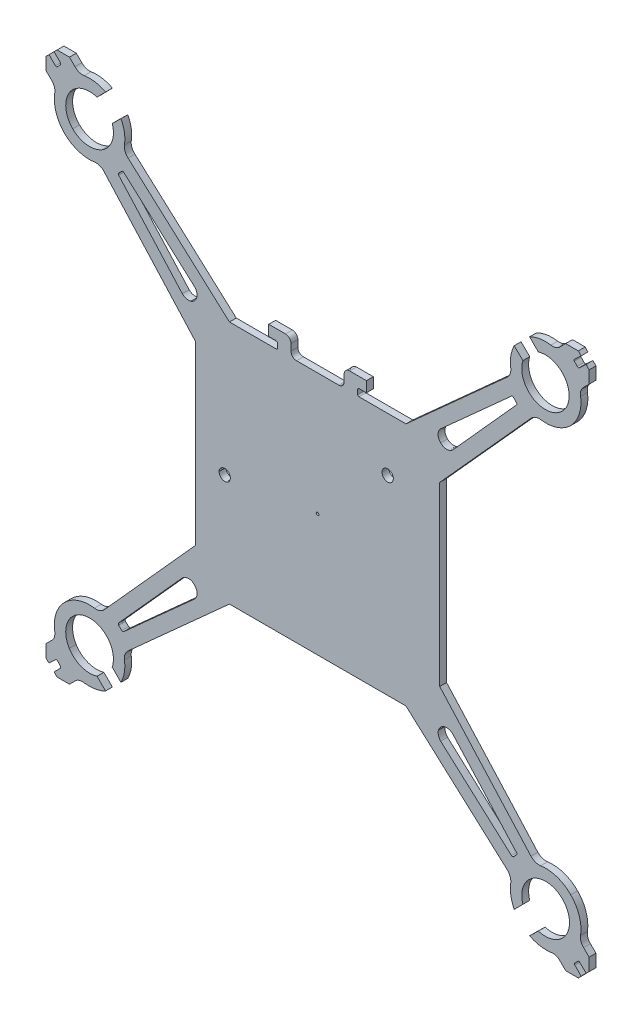
SolidWorks part; units mm, degrees
ref_plane "前视基准面" through (0, 0, 0) normal (0, 0, 1) x (1, 0, 0)
ref_plane "上视基准面" through (0, 0, 0) normal (0, 1, 0) x (1, 0, 0)
ref_plane "右视基准面" through (0, 0, 0) normal (1, 0, 0) x (0, 0, -1)
sketch "Model" plane through (0, 0, 0) normal (0, 0, 1) x (1, 0, 0)
  line L5 (274.707, 225.9985) -> (272.592, 225.9985)
  line L6 (271.5768, 227.0137) -> (271.5768, 228.2404)
  line L7 (270.5616, 229.2556) -> (267.4737, 229.2556)
  line L8 (267.4737, 229.2556) -> (267.4737, 227.3098)
  line L9 (267.4737, 227.3098) -> (268.8273, 227.3098)
  line L10 (269.0811, 227.056) -> (269.0811, 226.2523)
  line L11 (268.8273, 225.9985) -> (260.2404, 225.9985)
  line L12 (260.2404, 225.9985) -> (241.5861, 242.7916)
  line L13 (240.2748, 248.4175) -> (238.6674, 246.8524)
  line L14 (235.8756, 249.6442) -> (237.4407, 251.2516)
  line L15 (231.8148, 252.4783) -> (230.7996, 253.4935)
  line L16 (230.7996, 253.4935) -> (228.5154, 253.4935)
  line L17 (228.5154, 253.4935) -> (227.9655, 252.9436)
  line L18 (227.9655, 252.9436) -> (229.1499, 251.7592)
  line L19 (228.2193, 250.8286) -> (227.0349, 252.013)
  line L20 (227.0349, 252.013) -> (226.485, 251.4631)
  line L21 (226.485, 251.4631) -> (226.485, 249.1789)
  line L22 (226.485, 249.1789) -> (227.5002, 248.1637)
  line L23 (237.1869, 238.3924) -> (253.98, 219.7804)
  line L87 (253.98, 187.2517) -> (237.1869, 168.5974)
  line L88 (227.5002, 158.8684) -> (226.485, 157.8532)
  line L89 (226.485, 157.8532) -> (226.485, 155.5267)
  line L90 (226.485, 155.5267) -> (227.0349, 155.0191)
  line L91 (227.0349, 155.0191) -> (228.2193, 156.1612)
  line L92 (229.1499, 155.2729) -> (227.9655, 154.0885)
  line L93 (227.9655, 154.0885) -> (228.5154, 153.5386)
  line L94 (228.5154, 153.5386) -> (230.7996, 153.5386)
  line L95 (230.7996, 153.5386) -> (231.8148, 154.5538)
  line L96 (237.4407, 155.7805) -> (235.8756, 157.3456)
  line L97 (238.6674, 160.1797) -> (240.2748, 158.5723)
  line L98 (241.5861, 164.2405) -> (260.2404, 181.0336)
  line L99 (260.2404, 181.0336) -> (292.7268, 181.0336)
  line L100 (311.3811, 164.2405) -> (292.7268, 181.0336)
  line L101 (274.707, 225.9985) -> (278.2179, 225.9985)
  line L102 (253.98, 219.7804) -> (253.98, 187.2517)
  line L103 (298.9449, 219.7804) -> (298.9449, 187.2517)
  line L104 (253.98, 203.5161) -> (298.9449, 203.5161) construction
  line L105 (276.4624, 225.9985) -> (276.4836, 181.0336) construction
  line L106 (323.7307, 251.4898) -> (324.2582, 250.9184)
  line L107 (228.6, 250.8709) -> (229.1076, 251.4208)
  line L108 (239.8518, 239.5345) -> (240.444, 240.1267)
  line L109 (312.6501, 158.5723) -> (314.2575, 160.1797)
  line L110 (317.0916, 157.3456) -> (315.4842, 155.7805)
  line L111 (321.1101, 154.5538) -> (322.1253, 153.5386)
  line L112 (322.1253, 153.5386) -> (324.4518, 153.5386)
  line L113 (324.4518, 153.5386) -> (324.9594, 154.0885)
  line L114 (324.9594, 154.0885) -> (323.8173, 155.2729)
  line L115 (324.7056, 156.1612) -> (325.89, 155.0191)
  line L116 (325.89, 155.0191) -> (326.4399, 155.5267)
  line L117 (326.4399, 155.5267) -> (326.4399, 157.8532)
  line L118 (326.4399, 157.8532) -> (325.4247, 158.8684)
  line L119 (315.738, 168.5974) -> (298.9449, 187.2517)
  line L183 (298.9449, 219.7804) -> (315.738, 238.3924)
  line L184 (325.4247, 248.1637) -> (326.4399, 249.1789)
  line L185 (326.4399, 249.1789) -> (326.4399, 251.4631)
  line L186 (326.4399, 251.4631) -> (325.8903, 252.0585)
  line L187 (325.8903, 252.0585) -> (324.5946, 250.8626)
  line L188 (323.7504, 251.8276) -> (324.9594, 252.9436)
  line L189 (324.9594, 252.9436) -> (324.4518, 253.4935)
  line L190 (324.4518, 253.4935) -> (322.1253, 253.4935)
  line L191 (322.1253, 253.4935) -> (321.1101, 252.4783)
  line L192 (315.4842, 251.2516) -> (317.0916, 249.6442)
  line L193 (314.257, 246.8529) -> (312.6501, 248.4175)
  line L194 (311.3811, 242.7916) -> (292.7268, 225.9985)
  line L195 (292.7268, 225.9985) -> (284.0976, 225.9985)
  line L196 (283.8438, 226.2523) -> (283.8438, 227.056)
  line L197 (284.0976, 227.3098) -> (285.4512, 227.3098)
  line L198 (285.4512, 227.3098) -> (285.4512, 229.2556)
  line L199 (285.4512, 229.2556) -> (282.3633, 229.2556)
  line L200 (281.3481, 228.2404) -> (281.3481, 227.0137)
  line L201 (280.3752, 225.9985) -> (278.2179, 225.9985)
  line L217 (312.5232, 240.1267) -> (313.0731, 239.5345)
  line L218 (312.5232, 166.9054) -> (313.0731, 167.4553)
  line L220 (323.8173, 155.6113) -> (324.3672, 156.1612)
  line L221 (228.6, 156.1612) -> (229.1076, 155.6113)
  line L222 (239.8518, 167.4553) -> (240.444, 166.9054)
  line L223 (253.8108, 178.6225) -> (240.7824, 166.9054)
  line L224 (239.8518, 167.836) -> (251.5689, 180.8644)
  line L225 (314.2575, 246.8524) -> (316.161, 241.7341) construction
  line L226 (315.2092, 244.2933) -> (320.009, 246.0783) construction
  line L227 (322.1676, 247.783) -> (321.5331, 242.3686) construction
  line L228 (321.8503, 245.0758) -> (317.9231, 245.5361) construction
  line L229 (315.4842, 251.2516) -> (317.0916, 249.6442) construction
  line L231 (251.5689, 226.1677) -> (239.8518, 239.1961)
  line L232 (240.7824, 240.1267) -> (253.8108, 228.4096)
  line L233 (299.1141, 228.4096) -> (312.1425, 240.1267)
  line L234 (313.0731, 239.1961) -> (301.356, 226.1677)
  line L241 (301.356, 180.8644) -> (313.0731, 167.836)
  line L242 (312.1425, 166.9054) -> (299.1141, 178.6225)
  arc A0 (324.2582, 250.9184) -> (324.5946, 250.8626) centre (324.4623, 251.1067) ccw
  arc A1 (323.7504, 251.8276) -> (323.7307, 251.4898) centre (323.9157, 251.6485) ccw
  arc A3 (228.2193, 250.8286) -> (228.6, 250.8709) centre (228.3927, 251.0021) ccw
  arc A4 (229.1076, 251.4208) -> (229.1499, 251.7592) centre (228.8923, 251.6196) ccw
  arc A5 (240.444, 240.1267) -> (240.7824, 240.1267) centre (240.6132, 239.9575) cw
  arc A6 (239.8518, 239.5345) -> (239.8518, 239.1961) centre (240.021, 239.3653) ccw
  arc A7 (312.1425, 240.1267) -> (312.5232, 240.1267) centre (312.3329, 239.9151) cw
  arc A8 (313.0731, 239.5345) -> (313.0731, 239.1961) centre (312.8909, 239.3653) cw
  arc A9 (313.0731, 167.836) -> (313.0731, 167.4553) centre (312.8614, 167.6457) cw
  arc A10 (312.1425, 166.9054) -> (312.5232, 166.9054) centre (312.3329, 167.1171) ccw
  arc A11 (324.3672, 156.1612) -> (324.7056, 156.1612) centre (324.5364, 155.992) cw
  arc A12 (323.8173, 155.6113) -> (323.8173, 155.2729) centre (323.9865, 155.4421) ccw
  arc A13 (228.2193, 156.1612) -> (228.6, 156.1612) centre (228.4096, 155.9638) cw
  arc A14 (229.1076, 155.6113) -> (229.1499, 155.2729) centre (228.8923, 155.4126) cw
  arc A15 (239.8518, 167.836) -> (239.8518, 167.4553) centre (240.0635, 167.6457) ccw
  arc A16 (240.444, 166.9054) -> (240.7824, 166.9054) centre (240.6132, 167.0876) ccw
  arc A18 (314.257, 246.8529) -> (317.0916, 249.6442) centre (318.4005, 245.4801) ccw
  spline S3 degree 3 poles (272.592, 225.9985) (271.9998, 225.9985) (271.5768, 226.4215) (271.5768, 227.0137) knots 13 13 13 13 14 14 14 14
  spline S4 degree 3 poles (271.5768, 228.2404) (271.5768, 228.7903) (271.1115, 229.2556) (270.5616, 229.2556) knots 16 16 16 16 17 17 17 17
  spline S5 degree 3 poles (268.8273, 227.3098) (268.9542, 227.3098) (269.0811, 227.1829) (269.0811, 227.056) knots 21 21 21 21 22 22 22 22
  spline S6 degree 3 poles (269.0811, 226.2523) (269.0811, 226.1254) (268.9542, 225.9985) (268.8273, 225.9985) knots 24 24 24 24 25 25 25 25
  spline S7 degree 3 poles (241.5861, 242.7916) (241.0785, 243.2146) (240.8247, 243.8914) (240.9093, 244.5682) knots 28 28 28 28 29 29 29 29
  spline S8 degree 3 poles (240.9093, 244.5682) (241.1208, 245.8795) (240.9093, 247.2331) (240.2748, 248.4175) knots 30 30 30 30 31 31 31 31
  spline S9 degree 3 poles (238.6674, 246.8524) (239.3019, 244.9066) (238.5405, 242.7916) (236.8062, 241.7341) knots 33 33 33 33 34 34 34 34
  spline S10 degree 3 poles (236.8062, 241.7341) (235.0719, 240.6766) (232.83, 240.9304) (231.3918, 242.3686) knots 34 34 34 34 35 35 35 35
  spline S11 degree 3 poles (231.3918, 242.3686) (229.9536, 243.8068) (229.6998, 246.0487) (230.7573, 247.783) knots 35 35 35 35 36 36 36 36
  spline S12 degree 3 poles (230.7573, 247.783) (231.8148, 249.5173) (233.9298, 250.2787) (235.8756, 249.6442) knots 36 36 36 36 37 37 37 37
  spline S13 degree 3 poles (237.4407, 251.2516) (236.2563, 251.8861) (234.8604, 252.0976) (233.5068, 251.8861) knots 39 39 39 39 40 40 40 40
  spline S14 degree 3 poles (233.5068, 251.8861) (232.8723, 251.8015) (232.2378, 252.013) (231.8148, 252.4783) knots 41 41 41 41 42 42 42 42
  spline S20 degree 3 poles (227.5002, 248.1637) (227.9655, 247.7407) (228.177, 247.1062) (228.0924, 246.4717) knots 59 59 59 59 60 60 60 60
  spline S21 degree 3 poles (228.0924, 246.4717) (227.754, 244.4413) (228.4308, 242.3686) (229.869, 240.8881) knots 61 61 61 61 62 62 62 62
  spline S22 degree 3 poles (229.869, 240.8881) (231.3495, 239.4499) (233.3799, 238.7731) (235.4103, 239.0692) knots 62 62 62 62 63 63 63 63
  spline S23 degree 3 poles (235.4103, 239.0692) (236.0871, 239.1538) (236.7639, 238.9) (237.1869, 238.3924) knots 64 64 64 64 65 65 65 65
  spline S72 degree 3 poles (237.1869, 168.5974) (236.7639, 168.1321) (236.0871, 167.8783) (235.4103, 167.9629) knots 221 221 221 221 222 222 222 222
  spline S73 degree 3 poles (235.4103, 167.9629) (233.3799, 168.259) (231.3495, 167.5822) (229.869, 166.1017) knots 223 223 223 223 224 224 224 224
  spline S74 degree 3 poles (229.869, 166.1017) (228.4308, 164.6635) (227.754, 162.5908) (228.0924, 160.5604) knots 224 224 224 224 225 225 225 225
  spline S75 degree 3 poles (228.0924, 160.5604) (228.177, 159.9259) (227.9655, 159.2914) (227.5002, 158.8684) knots 226 226 226 226 227 227 227 227
  spline S81 degree 3 poles (231.8148, 154.5538) (232.2378, 155.0191) (232.8723, 155.2306) (233.5068, 155.1037) knots 244 244 244 244 245 245 245 245
  spline S82 degree 3 poles (233.5068, 155.1037) (234.8604, 154.9345) (236.2563, 155.146) (237.4407, 155.7805) knots 246 246 246 246 247 247 247 247
  spline S83 degree 3 poles (235.8756, 157.3456) (233.9298, 156.7534) (231.8148, 157.5148) (230.7573, 159.2491) knots 249 249 249 249 250 250 250 250
  spline S84 degree 3 poles (230.7573, 159.2491) (229.6998, 160.9834) (229.9536, 163.2253) (231.3918, 164.6635) knots 250 250 250 250 251 251 251 251
  spline S85 degree 3 poles (231.3918, 164.6635) (232.83, 166.1017) (235.0719, 166.3555) (236.8062, 165.298) knots 251 251 251 251 252 252 252 252
  spline S86 degree 3 poles (236.8062, 165.298) (238.5405, 164.2405) (239.3019, 162.1255) (238.6674, 160.1797) knots 252 252 252 252 253 253 253 253
  spline S87 degree 3 poles (240.2748, 158.5723) (240.9093, 159.799) (241.1208, 161.1526) (240.9093, 162.4639) knots 255 255 255 255 256 256 256 256
  spline S88 degree 3 poles (240.9093, 162.4639) (240.8247, 163.1407) (241.0785, 163.7752) (241.5861, 164.2405) knots 257 257 257 257 258 258 258 258
  spline S93 degree 3 poles (311.3811, 164.2405) (311.8464, 163.7752) (312.1002, 163.1407) (312.0156, 162.4639) knots 278 278 278 278 279 279 279 279
  spline S94 degree 3 poles (312.0156, 162.4639) (311.8041, 161.1526) (312.0579, 159.799) (312.6501, 158.5723) knots 280 280 280 280 281 281 281 281
  spline S95 degree 3 poles (314.2575, 160.1797) (313.623, 162.1255) (314.4267, 164.2405) (316.161, 165.298) knots 283 283 283 283 284 284 284 284
  spline S96 degree 3 poles (316.161, 165.298) (317.8953, 166.3555) (320.0949, 166.1017) (321.5331, 164.6635) knots 284 284 284 284 285 285 285 285
  spline S97 degree 3 poles (321.5331, 164.6635) (322.9713, 163.2253) (323.2674, 160.9834) (322.1676, 159.2491) knots 285 285 285 285 286 286 286 286
  spline S98 degree 3 poles (322.1676, 159.2491) (321.1101, 157.5148) (318.9951, 156.7534) (317.0916, 157.3456) knots 286 286 286 286 287 287 287 287
  spline S99 degree 3 poles (315.4842, 155.7805) (316.7109, 155.146) (318.0645, 154.9345) (319.4181, 155.1037) knots 289 289 289 289 290 290 290 290
  spline S100 degree 3 poles (319.4181, 155.1037) (320.0526, 155.2306) (320.6871, 155.0191) (321.1101, 154.5538) knots 291 291 291 291 292 292 292 292
  spline S106 degree 3 poles (325.4247, 158.8684) (324.9594, 159.2914) (324.7479, 159.9259) (324.8748, 160.5604) knots 309 309 309 309 310 310 310 310
  spline S107 degree 3 poles (324.8748, 160.5604) (325.1709, 162.5908) (324.4941, 164.6635) (323.0559, 166.1017) knots 311 311 311 311 312 312 312 312
  spline S108 degree 3 poles (323.0559, 166.1017) (321.6177, 167.5822) (319.545, 168.259) (317.5146, 167.9629) knots 312 312 312 312 313 313 313 313
  spline S109 degree 3 poles (317.5146, 167.9629) (316.8378, 167.8783) (316.2033, 168.1321) (315.738, 168.5974) knots 314 314 314 314 315 315 315 315
  spline S158 degree 3 poles (315.738, 238.3924) (316.2033, 238.9) (316.8378, 239.1538) (317.5146, 239.0692) knots 471 471 471 471 472 472 472 472
  spline S159 degree 3 poles (317.5146, 239.0692) (319.545, 238.7731) (321.6177, 239.4499) (323.0559, 240.8881) knots 473 473 473 473 474 474 474 474
  spline S160 degree 3 poles (323.0559, 240.8881) (324.4941, 242.3686) (325.1709, 244.4413) (324.8748, 246.4717) knots 474 474 474 474 475 475 475 475
  spline S161 degree 3 poles (324.8748, 246.4717) (324.7479, 247.1062) (324.9594, 247.7407) (325.4247, 248.1637) knots 476 476 476 476 477 477 477 477
  spline S167 degree 3 poles (321.1101, 252.4783) (320.6871, 252.013) (320.0526, 251.8015) (319.4181, 251.8861) knots 494 494 494 494 495 495 495 495
  spline S168 degree 3 poles (319.4181, 251.8861) (318.0645, 252.0976) (316.7109, 251.8861) (315.4842, 251.2516) knots 496 496 496 496 497 497 497 497
  spline S173 degree 3 poles (312.6501, 248.4175) (312.0579, 247.2331) (311.8041, 245.8795) (312.0156, 244.5682) knots 505 505 505 505 506 506 506 506
  spline S174 degree 3 poles (312.0156, 244.5682) (312.1002, 243.8914) (311.8464, 243.2146) (311.3811, 242.7916) knots 507 507 507 507 508 508 508 508
  spline S175 degree 3 poles (284.0976, 225.9985) (283.9707, 225.9985) (283.8438, 226.1254) (283.8438, 226.2523) knots 511 511 511 511 512 512 512 512
  spline S176 degree 3 poles (283.8438, 227.056) (283.8438, 227.1829) (283.9707, 227.3098) (284.0976, 227.3098) knots 514 514 514 514 515 515 515 515
  spline S177 degree 3 poles (282.3633, 229.2556) (281.8134, 229.2556) (281.3481, 228.7903) (281.3481, 228.2404) knots 519 519 519 519 520 520 520 520
  spline S178 degree 3 poles (281.3481, 227.0137) (281.3481, 226.4215) (280.9251, 225.9985) (280.3752, 225.9985) knots 522 522 522 522 523 523 523 523
  spline S196 degree 3 poles (251.5689, 180.8644) (251.9919, 181.2451) (252.5841, 181.4143) (253.134, 181.2874) knots 9 9 9 9 10 10 10 10
  spline S197 degree 3 poles (253.134, 181.2874) (253.6416, 181.1182) (254.0646, 180.6952) (254.2338, 180.1453) knots 10 10 10 10 11 11 11 11
  spline S198 degree 3 poles (254.2338, 180.1453) (254.3607, 179.5954) (254.2338, 179.0455) (253.8108, 178.6225) knots 11 11 11 11 12 12 12 12
  spline S205 degree 3 poles (253.8108, 228.4096) (254.2338, 227.9866) (254.3607, 227.3944) (254.2338, 226.8868) knots 1 1 1 1 2 2 2 2
  spline S206 degree 3 poles (254.2338, 226.8868) (254.0646, 226.3369) (253.6416, 225.9139) (253.134, 225.7447) knots 2 2 2 2 3 3 3 3
  spline S207 degree 3 poles (253.134, 225.7447) (252.5841, 225.6178) (251.9919, 225.7447) (251.5689, 226.1677) knots 3 3 3 3 4 4 4 4
  spline S214 degree 3 poles (301.356, 226.1677) (300.7215, 225.5332) (299.7486, 225.5332) (299.1141, 226.1677) knots 9 9 9 9 10 10 10 10
  spline S215 degree 3 poles (299.1141, 226.1677) (298.4796, 226.7599) (298.4796, 227.7751) (299.1141, 228.4096) knots 10 10 10 10 11 11 11 11
  spline S222 degree 3 poles (299.1141, 178.6225) (298.7334, 179.0455) (298.5642, 179.5954) (298.6911, 180.1453) knots 1 1 1 1 2 2 2 2
  spline S223 degree 3 poles (298.6911, 180.1453) (298.8603, 180.6952) (299.2833, 181.1182) (299.8332, 181.2874) knots 2 2 2 2 3 3 3 3
  spline S224 degree 3 poles (299.8332, 181.2874) (300.3831, 181.4143) (300.933, 181.2451) (301.356, 180.8644) knots 3 3 3 3 4 4 4 4
  spline S234 degree 3 poles (258.3369, 201.2107) (258.3369, 201.7606) (258.8022, 202.2259) (259.3944, 202.2259) (259.9443, 202.2259) (260.4096, 201.7606) (260.4096, 201.2107) knots 2 2 2 2 3 3 3 4 4 4 4
  spline S235 degree 3 poles (260.4096, 201.2107) (260.4096, 200.6185) (259.9443, 200.1532) (259.3944, 200.1532) (258.8022, 200.1532) (258.3369, 200.6185) (258.3369, 201.2107) knots 0 0 0 0 1 1 1 2 2 2 2
  spline S236 degree 3 poles (288.3276, 216.1003) (288.3276, 216.6925) (288.7929, 217.1578) (289.3428, 217.1578) (289.935, 217.1578) (290.4003, 216.6925) (290.4003, 216.1003) knots 2 2 2 2 3 3 3 4 4 4 4
  spline S237 degree 3 poles (290.4003, 216.1003) (290.4003, 215.5081) (289.935, 215.0428) (289.3428, 215.0428) (288.7929, 215.0428) (288.3276, 215.5081) (288.3276, 216.1003) knots 0 0 0 0 1 1 1 2 2 2 2
extrude "凸台-拉伸1" add sketch "Model" along normal blind 1.26
sketch "草图1" plane through (0, 0, 1.26) normal (0, 0, 1) x (1, 0, 0)
  line L0 (253.98, 203.5161) -> (298.9449, 203.5161) construction
  line L1 (253.98, 219.7804) -> (253.98, 187.2517) construction
  line L2 (298.9449, 187.2517) -> (298.9449, 219.7804) construction
  line L3 (276.4836, 225.9985) -> (276.4836, 181.0336) construction
  line L4 (280.3752, 225.9985) -> (272.592, 225.9985) construction
  line L5 (260.2404, 181.0336) -> (292.7268, 181.0336) construction
  circle A0 centre (276.4624, 203.5161) radius 0.25
  dimension "D1" = 0.5
extrude "切除-拉伸1" cut sketch "草图1" against normal through all
